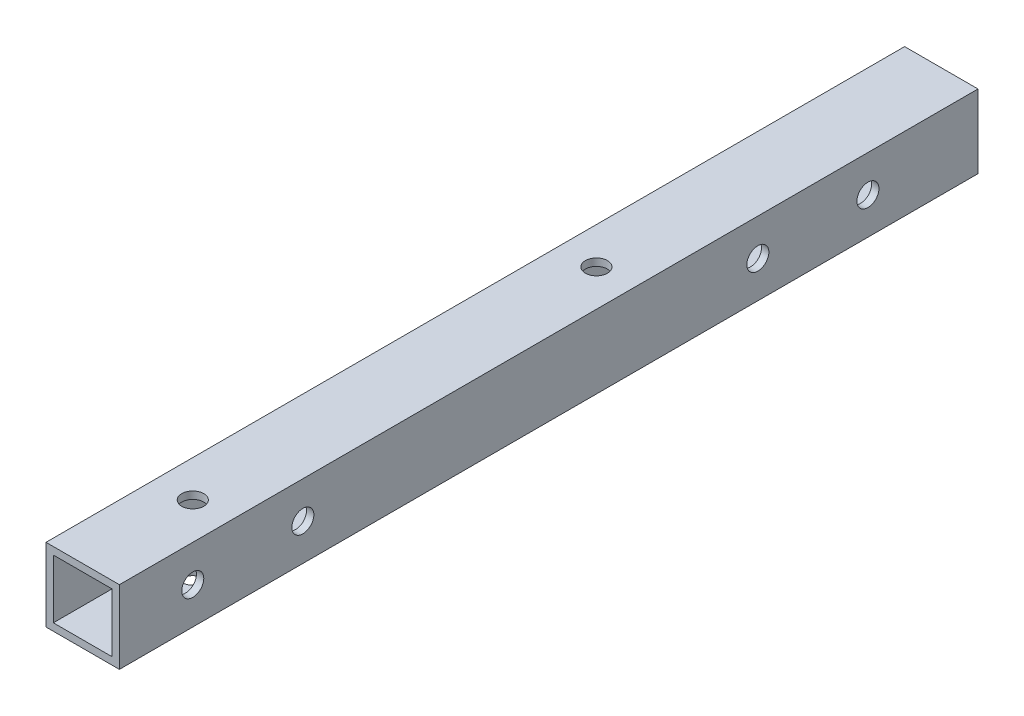
SolidWorks part; units mm, degrees
material "6063-O"
ref_plane "前视基准面" through (0, 0, 0) normal (0, 0, 1) x (1, 0, 0)
ref_plane "上视基准面" through (0, 0, 0) normal (0, 1, 0) x (1, 0, 0)
ref_plane "右视基准面" through (0, 0, 0) normal (1, 0, 0) x (0, 0, -1)
other "Configuration Table"
sketch "草图1" plane through (0, 0, 0) normal (0, 0, 1) x (1, 0, 0)
  line L1 (-5, -5) -> (5, -5)
  line L2 (-5, -5) -> (-5, 5)
  line L3 (-5, 5) -> (5, 5)
  line L4 (5, -5) -> (5, 5)
  line L5 (-5, -5) -> (5, 5) construction
  line L6 (-5, 5) -> (5, -5) construction
  point P4 (0, 0)
  dimension "D1" = 10
  dimension "D2" = 10
extrude "拉伸-薄壁1" add sketch "草图1" along normal blind 117 thin thin type one direction reverse wall 1
sketch "草图2" plane through (5, 0, 0) normal (1, 0, 0) x (0, 0, -1)
  line L0 (0, 0) -> (-117, 0) construction
  line L1 (-117, -5) -> (-117, 5) construction
  circle A0 centre (-15, 0) radius 1.5
  circle A1 centre (-30, 0) radius 1.5
  circle A2 centre (-107, 0) radius 1.5
  circle A3 centre (-92, 0) radius 1.5
  dimension "D1" = 3
  dimension "D3" = 15
  dimension "D4" = 10
  dimension "D5" = 15
  dimension "D2" = 15
extrude "切除-拉伸1" cut sketch "草图2" against normal through all
sketch "草图3" plane through (0, -5, 0) normal (0, -1, 0) x (1, 0, 0)
  line L0 (0, 117) -> (0, 49.8065) construction
  line L1 (-5, 117) -> (5, 117) construction
  circle A0 centre (0, 102) radius 1.5
  circle A1 centre (0, 47) radius 1.5
  dimension "D1" = 3
  dimension "D2" = 55
  dimension "D3" = 15
extrude "切除-拉伸2" cut sketch "草图3" against normal blind 10
